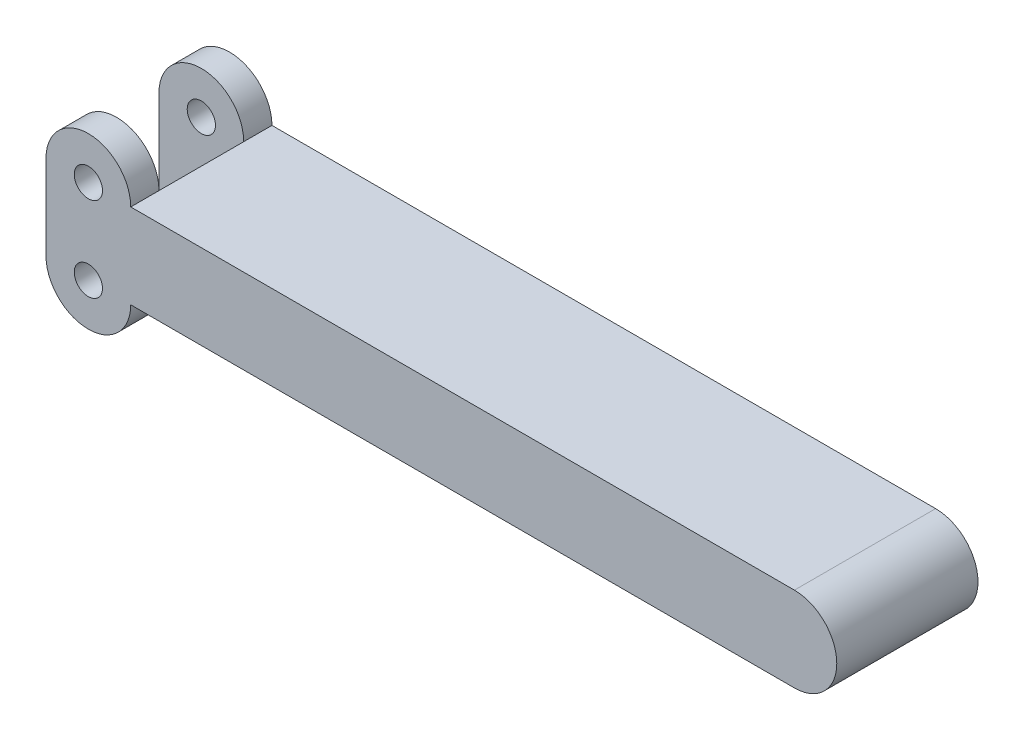
SolidWorks part; units mm, degrees
ref_plane "Front Plane" through (0, 0, 0) normal (0, 0, 1) x (1, 0, 0)
ref_plane "Top Plane" through (0, 0, 0) normal (0, 1, 0) x (1, 0, 0)
ref_plane "Right Plane" through (0, 0, 0) normal (1, 0, 0) x (0, 0, -1)
sketch "Sketch1" plane through (0, 0, 0) normal (0, 0, 1) x (1, 0, 0)
  line L0 (0, 0) -> (0, 19.05) construction
  line L1 (-9.525, 0) -> (-9.525, 19.05)
  line L2 (9.525, 0) -> (9.525, 19.05)
  line L3 (9.525, 19.05) -> (158.75, 19.05)
  line L5 (158.75, 0) -> (9.525, 0)
  line L6 (9.525, 19.05) -> (9.525, 0)
  arc A0 (-9.525, 0) -> (9.525, 0) centre (0, 0) ccw
  arc A1 (9.525, 19.05) -> (-9.525, 19.05) centre (0, 19.05) ccw
  circle A2 centre (0, 19.05) radius 3.175
  circle A3 centre (0, 0) radius 3.175
  arc A4 (158.75, 0) -> (158.75, 19.05) centre (158.75, 9.525) ccw
  point P3 (0, 9.525)
  dimension "D3" = 6.35
  dimension "D4" = 6.35
  dimension "D7" = 19.05
  dimension "D1" = 19.05
  dimension "D2" = 9.525
  dimension "D5" = 149.225
extrude "Boss-Extrude1" add sketch "Sketch1" along normal blind 31.75
sketch "Sketch6" plane through (-9.525, 0, 0) normal (-1, 0, 0) x (0, 0, 1)
  line L0 (0, 0) -> (0, -9.525) construction
  line L1 (0, 0) -> (31.75, 0) construction
  line L2 (31.75, -9.525) -> (31.75, 0) construction
  line L3 (0, 19.05) -> (0, 0) construction
  line L4 (31.75, 0) -> (31.75, 19.05) construction
  line L5 (0, 28.575) -> (0, 19.05) construction
  line L6 (31.75, 19.05) -> (31.75, 28.575) construction
  line L7 (31.75, 19.05) -> (0, 19.05) construction
  line L8 (0, 0) -> (0, -9.525)
  line L9 (0, 0) -> (31.75, 0)
  line L10 (31.75, -9.525) -> (31.75, 0)
  line L11 (0, 19.05) -> (0, 0)
  line L12 (31.75, 0) -> (31.75, 19.05)
  line L13 (0, 28.575) -> (0, 19.05)
  line L14 (31.75, 19.05) -> (31.75, 28.575)
  line L15 (31.75, 19.05) -> (0, 19.05)
  line L16 (31.75, 28.575) -> (0, 28.575) construction
  line L17 (6.35, 28.575) -> (25.4, 28.575)
  line L18 (6.35, 28.575) -> (6.35, -9.525)
  line L19 (6.35, -9.525) -> (25.4, -9.525)
  line L20 (25.4, 28.575) -> (25.4, -9.525)
  line L21 (0, -9.525) -> (31.75, -9.525) construction
  dimension "D1" = 19.05
  dimension "D2" = 6.35
extrude "Cut-Extrude1" cut sketch "Sketch6" against normal blind 19.05 contours L20 L15 L18 L9 | L20 L17 L18 L15 | L20 L9 L18 L19
